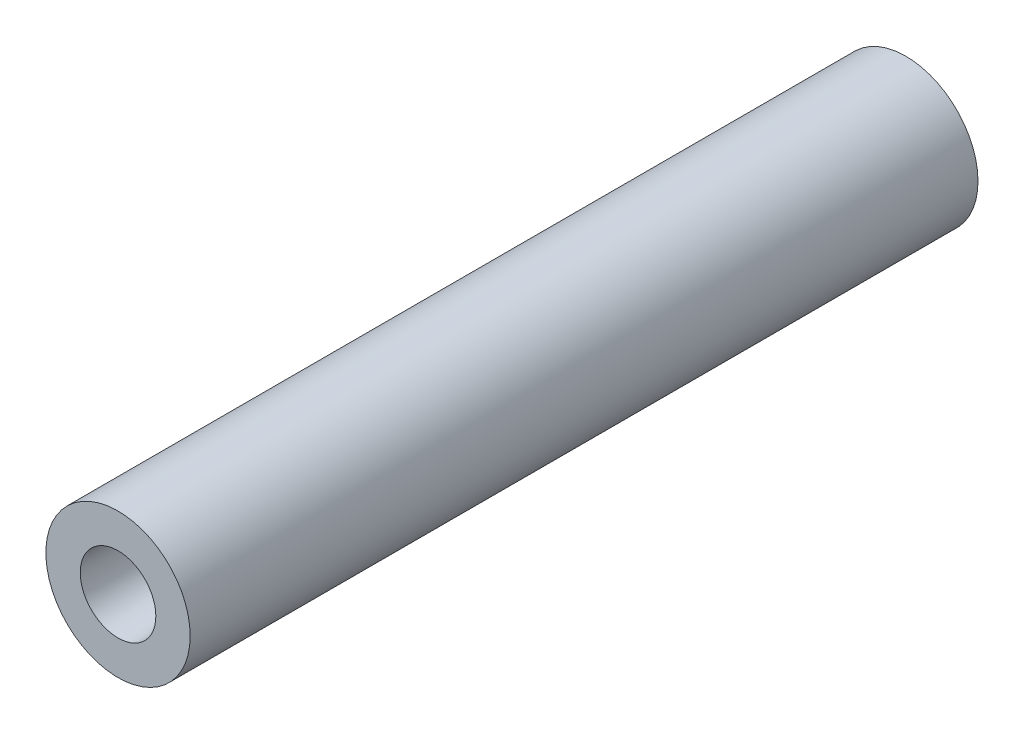
SolidWorks part; units mm, degrees
ref_plane "Front Plane" through (0, 0, 0) normal (0, 0, 1) x (1, 0, 0)
ref_plane "Top Plane" through (0, 0, 0) normal (0, 1, 0) x (1, 0, 0)
ref_plane "Right Plane" through (0, 0, 0) normal (1, 0, 0) x (0, 0, -1)
sketch "Sketch1" plane through (0, 0, 0) normal (0, 0, 1) x (1, 0, 0)
  circle A0 centre (0, 0) radius 6
  dimension "D1" = 12
extrude "Boss-Extrude1" add sketch "Sketch1" along normal blind 65.5
sketch "Sketch2" plane through (0, 0, 0) normal (0, 0, 1) x (1, 0, 0)
  circle A0 centre (0, 0) radius 1
extrude "Cut-Extrude1" cut sketch "Sketch2" along normal through all
sketch "Sketch3" plane through (0, 0, 0) normal (0, 0, 1) x (1, 0, 0)
  circle A0 centre (0, 0) radius 3.1433
  dimension "D1" = 6.2865
extrude "Cut-Extrude2" cut sketch "Sketch3" along normal blind 9.0297 draft 2.328
sketch "Sketch4" plane through (0, 0, 65.5) normal (0, 0, 1) x (1, 0, 0)
  circle A0 centre (0, 0) radius 3.1433
  circle A1 centre (0, 0) radius 3.1433 construction
extrude "Cut-Extrude3" cut sketch "Sketch4" against normal blind 9.0297 draft 2.328 contours A0
